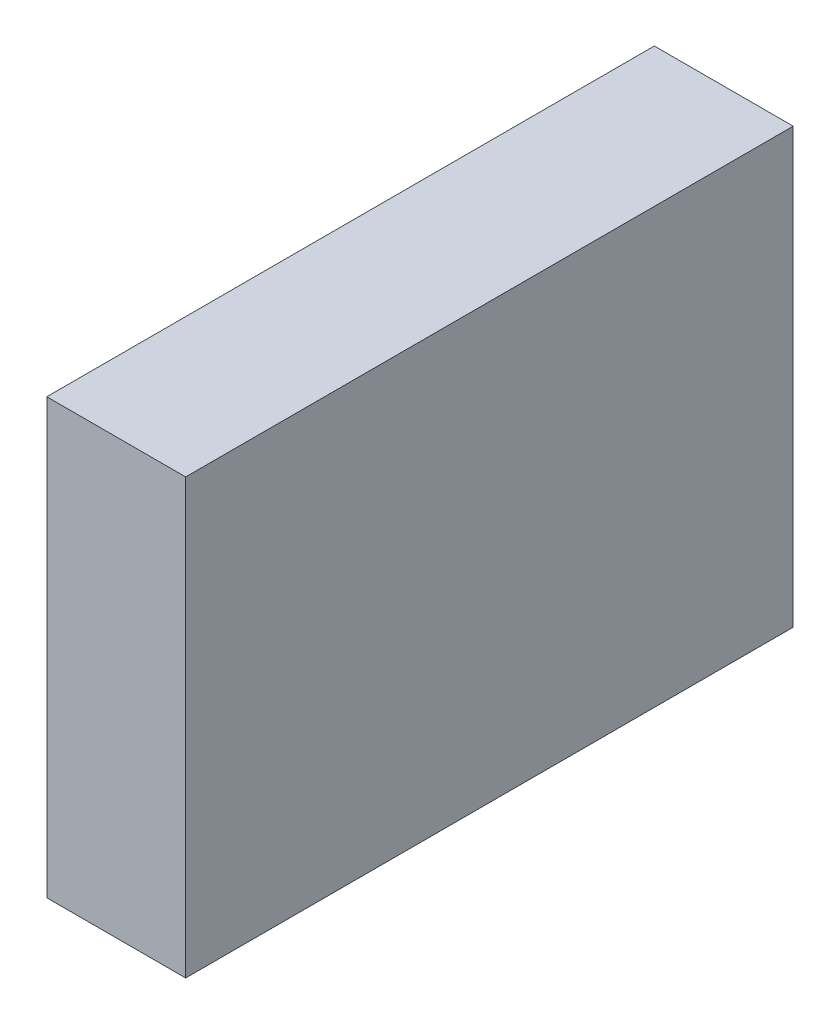
SolidWorks part; units mm, degrees
ref_plane "Front Plane" through (0, 0, 0) normal (0, 0, 1) x (1, 0, 0)
ref_plane "Top Plane" through (0, 0, 0) normal (0, 1, 0) x (1, 0, 0)
ref_plane "Right Plane" through (0, 0, 0) normal (1, 0, 0) x (0, 0, -1)
sketch "Sketch1" plane through (0, 0, 0) normal (1, 0, 0) x (0, 0, -1)
  line L1 (-17.5, -12.5) -> (17.5, -12.5)
  line L2 (-17.5, -12.5) -> (-17.5, 12.5)
  line L3 (-17.5, 12.5) -> (17.5, 12.5)
  line L4 (17.5, -12.5) -> (17.5, 12.5)
  line L5 (-17.5, -12.5) -> (17.5, 12.5) construction
  line L6 (-17.5, 12.5) -> (17.5, -12.5) construction
  point P0 (0, 0)
  dimension "D1" = 35
  dimension "D2" = 25
extrude "Boss-Extrude1" add sketch "Sketch1" along normal blind 8
